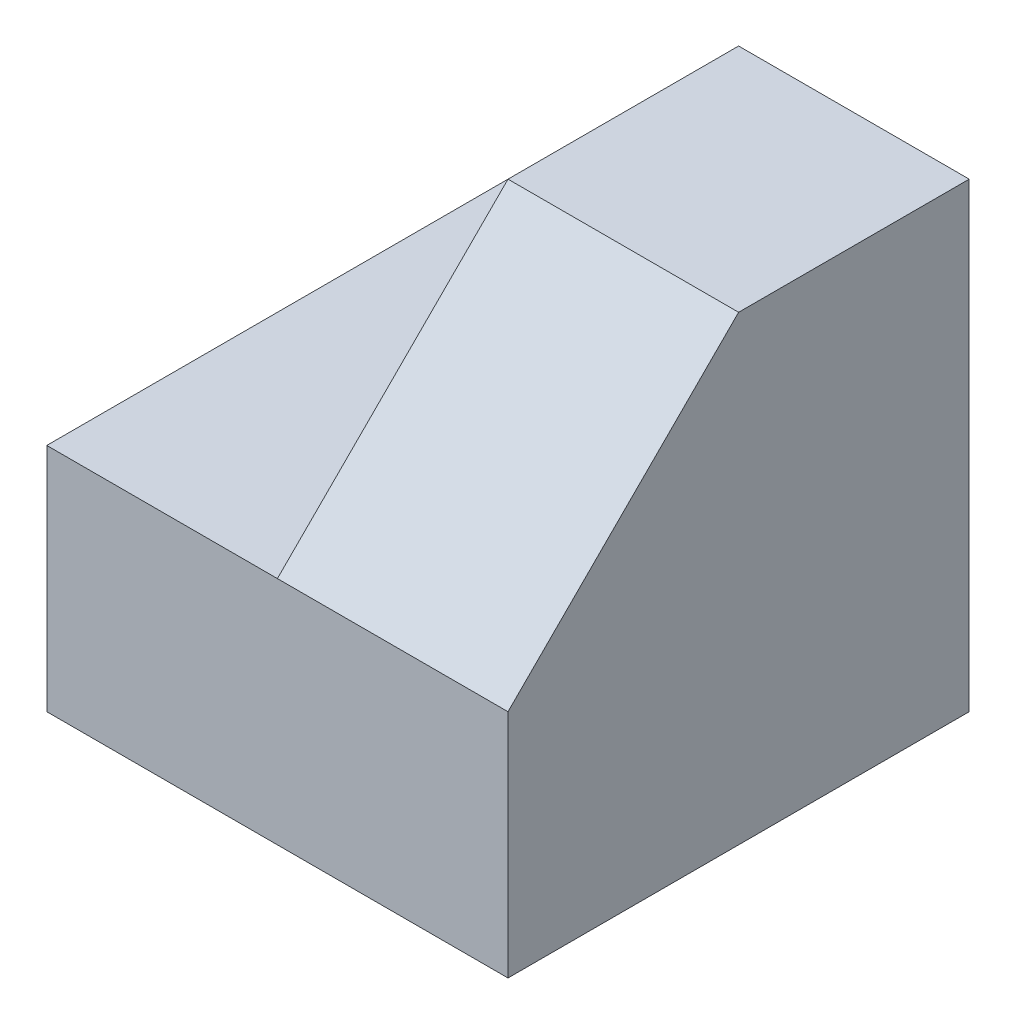
SolidWorks part; units mm, degrees
ref_plane "Front Plane" through (0, 0, 0) normal (0, 0, 1) x (1, 0, 0)
ref_plane "Top Plane" through (0, 0, 0) normal (0, 1, 0) x (1, 0, 0)
ref_plane "Right Plane" through (0, 0, 0) normal (1, 0, 0) x (0, 0, -1)
sketch "Sketch1" plane through (0, 0, 0) normal (0, 0, 1) x (1, 0, 0)
  line L1 (0, 0) -> (40, 0)
  line L2 (0, 0) -> (0, 40)
  line L3 (0, 40) -> (40, 40)
  line L4 (40, 0) -> (40, 40)
  dimension "D1" = 40
  dimension "D2" = 40
extrude "Boss-Extrude1" add sketch "Sketch1" along normal blind 40
sketch "Sketch2" plane through (0, 0, 40) normal (0, 0, 1) x (1, 0, 0)
  line L1 (0, 40) -> (20, 40)
  line L2 (0, 40) -> (0, 20)
  line L3 (0, 20) -> (20, 20)
  line L4 (20, 40) -> (20, 20)
  dimension "D1" = 20
  dimension "D2" = 20
extrude "Cut-Extrude1" cut sketch "Sketch2" against normal blind 40
sketch "Sketch3" plane through (20, 0, 0) normal (-1, 0, 0) x (0, 0, 1)
  line L0 (20, 40) -> (40, 20)
  line L1 (0, 40) -> (40, 40) construction
  line L2 (40, 20) -> (40, 40)
  line L3 (40, 40) -> (20, 40)
extrude "Cut-Extrude2" cut sketch "Sketch3" against normal blind 40
